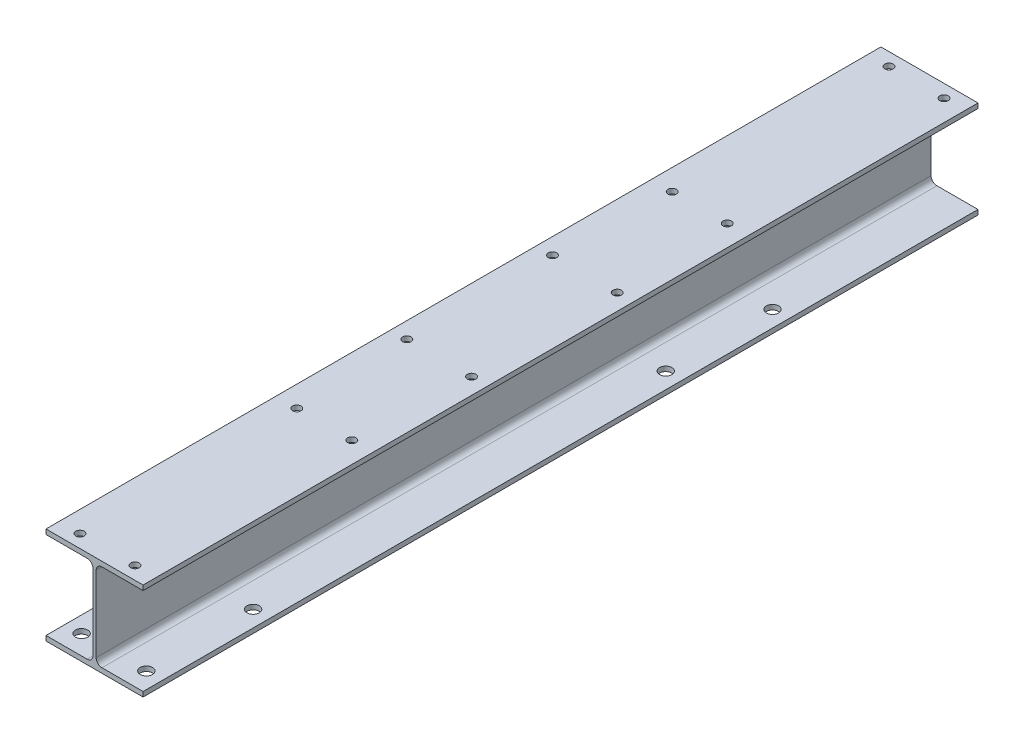
SolidWorks part; units mm, degrees
ref_plane "Спереди" through (0, 0, 0) normal (0, 0, 1) x (1, 0, 0)
ref_plane "Сверху" through (0, 0, 0) normal (0, 1, 0) x (1, 0, 0)
ref_plane "Справа" through (0, 0, 0) normal (1, 0, 0) x (0, 0, -1)
sketch "Эскиз1" plane through (0, 0, 0) normal (0, 0, 1) x (1, 0, 0)
  line L1 (150, 300) -> (-150, 300)
  line L2 (-150, 300) -> (-150, 285)
  line L3 (-150, 285) -> (-23, 285)
  line L4 (-5, 267) -> (-5, 33)
  line L5 (-23, 15) -> (-150, 15)
  line L6 (-150, 15) -> (-150, 0)
  line L7 (-150, 0) -> (150, 0)
  line L8 (150, 0) -> (150, 15)
  line L9 (150, 15) -> (23, 15)
  line L10 (5, 33) -> (5, 267)
  line L11 (23, 285) -> (150, 285)
  line L12 (150, 285) -> (150, 300)
  arc A0 (-5, 267) -> (-23, 285) centre (-23, 267) ccw
  arc A1 (-23, 15) -> (-5, 33) centre (-23, 33) ccw
  arc A2 (5, 33) -> (23, 15) centre (23, 33) ccw
  arc A3 (23, 285) -> (5, 267) centre (23, 267) ccw
extrude "Бобышка-Вытянуть1" add sketch "Эскиз1" along normal mid plane 2580
sketch "Эскиз2" plane through (0, 0, 0) normal (0, -1, 0) x (1, 0, 0)
  circle A0 centre (-100, 1230) radius 19
  circle A1 centre (100, 1230) radius 19
  circle A2 centre (-100, 900) radius 19
  circle A3 centre (100, 900) radius 19
  circle A4 centre (-100, -705) radius 19
  circle A5 centre (100, -705) radius 19
  circle A6 centre (-100, -375) radius 19
  circle A7 centre (100, -375) radius 19
extrude "Вырез-Вытянуть1" cut sketch "Эскиз2" against normal blind 60
sketch "Эскиз3" plane through (0, 300, 0) normal (0, 1, 0) x (1, 0, 0)
  circle A0 centre (-85, -1250) radius 13
  circle A1 centre (85, -1250) radius 13
  circle A2 centre (-85, -580) radius 13
  circle A3 centre (85, -580) radius 13
  circle A4 centre (-100, -225) radius 13
  circle A5 centre (100, -225) radius 13
  circle A6 centre (-100, 225) radius 13
  circle A7 centre (100, 225) radius 13
  circle A8 centre (-85, 580) radius 13
  circle A9 centre (85, 580) radius 13
  circle A10 centre (-85, 1250) radius 13
  circle A11 centre (85, 1250) radius 13
extrude "Вырез-Вытянуть2" cut sketch "Эскиз3" against normal blind 60
